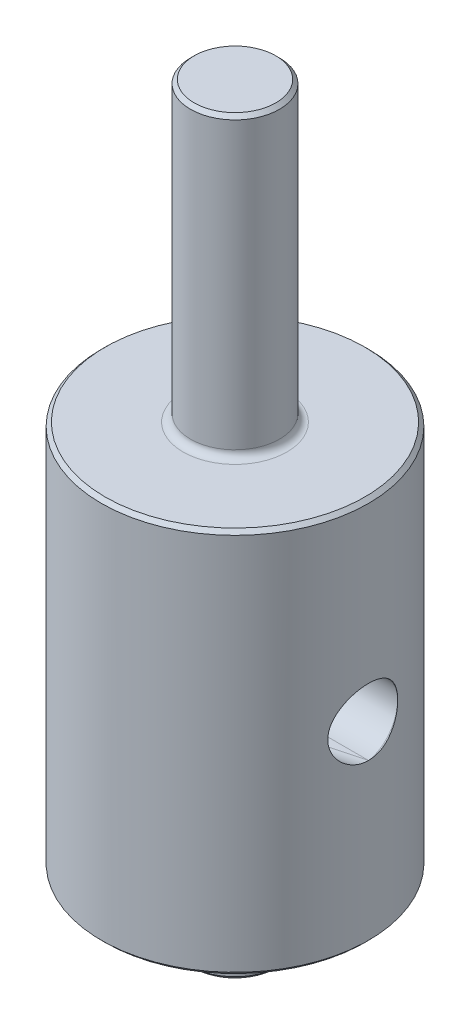
SolidWorks part; units mm, degrees
material "AISI 316 Barra de aço inoxidável recozido (SS)"
ref_plane "Plano frontal" through (0, 0, 0) normal (0, 0, 1) x (1, 0, 0)
ref_plane "Plano superior" through (0, 0, 0) normal (0, 1, 0) x (1, 0, 0)
ref_plane "Plano direito" through (0, 0, 0) normal (1, 0, 0) x (0, 0, -1)
sketch "Esboço1" plane through (0, 0, 0) normal (0, 0, 1) x (1, 0, 0)
  line L0 (0, 0) -> (0, 26.74) construction
  line L1 (0, 0) -> (9, 0) construction
  line L2 (0, 33) -> (3, 33)
  line L3 (3, 13) -> (3, 33)
  line L4 (9, 13) -> (3, 13)
  line L11 (9, 13) -> (9, -13)
  line L12 (0, 33) -> (0, 0)
  line L17 (3, -13) -> (9, -13)
  line L18 (3, -17.5) -> (3, -13)
  line L21 (3, -17.5) -> (0, -17.5)
  line L22 (0, -17.5) -> (0, 0)
  point P16 (9, 0)
  dimension "D1" = 6
  dimension "D2" = 6
  dimension "D5" = 18
  dimension "D6" = 20
  dimension "D7" = 26
  dimension "D9" = 4.5
revolve "Revolução1" add sketch "Esboço1" angle 360 about L0
ref_plane "Plano1" through (-9, 0, 0) normal (-1, 0, 0) x (0, 0, 1)
ref_plane "Plano2" through (9, 0, 0) normal (1, 0, 0) x (0, 0, -1)
sketch "Esboço2" plane through (-9, 0, 0) normal (-1, 0, 0) x (0, 0, 1)
  circle A0 centre (0, 0) radius 2.25
  dimension "D1" = 4.5
extrude "Corte-extrusão2" cut sketch "Esboço2" against normal through all
sketch "Esboço4" plane through (0, 0, 0) normal (0, 1, 0) x (1, 0, 0)
  line L0 (9, 0) -> (-9, 0)
  line L1 (0, 0) -> (-7.7942, -4.5) construction
  line L2 (9, 0) -> (-7.7942, -4.5)
  arc A0 (8.7142, -2.25) -> (8.7142, 2.25) centre (0, 0) ccw construction
  circle A1 centre (0, 0) radius 9 construction
  dimension "D1" = 30
ref_plane "Plano3" through (-7.7942, 0, 4.5) normal (-0.9659, 0, 0.2588) x (0.2588, 0, 0.9659)
sketch "Esboço7" plane through (-7.7942, 0, 4.5) normal (-0.9659, 0, 0.2588) x (0.2588, 0, 0.9659)
  circle A0 centre (0, 0) radius 2.25
  dimension "D1" = 4.5
extrude "Corte-extrusão6" cut sketch "Esboço7" against normal through all both and the other way through all
sketch "Sketch1" plane through (0, 0, 0) normal (0, 1, 0) x (1, 0, 0)
  line L0 (9, 0) -> (-10.8444, 0)
  line L1 (-10.8444, 0) -> (-10.4288, -5.2059)
  line L2 (-10.4288, -5.2059) -> (9, 0)
  line L3 (9, 0) -> (-7.7942, -4.5) construction
extrude "Cut-Extrude1" cut sketch "Sketch1" against normal mid plane 4.5
sketch "Sketch2" plane through (0, 0, 0) normal (0, 0, 1) x (1, 0, 0)
  line L0 (8.5, -13) -> (9, 13)
  line L1 (-9, -13) -> (9, -13) construction
  line L2 (9, -9.9) -> (9, 9.9) construction
  line L3 (9, 13) -> (-9, 13) construction
  line L4 (9, 13) -> (9, -13)
  line L5 (9, -13) -> (8.5, -13)
  dimension "D1" = 0.5
revolve "Cut-Revolve1" [suppressed] cut sketch "Sketch2" angle 360
fillet "Fillet1" radius 0.5 2 edges at (0, -13, -3) (0, 13, -3)
chamfer "Chamfer1" distance 0.25 angle 45 2 edges at (0, -17.5, -3) (0, 33, -3)
chamfer "Chamfer3" [suppressed] distance 0.25 angle 45
chamfer "Chamfer4" distance 0.25 angle 45 2 edges at (0, -13, -9) (0, 13, -9)
